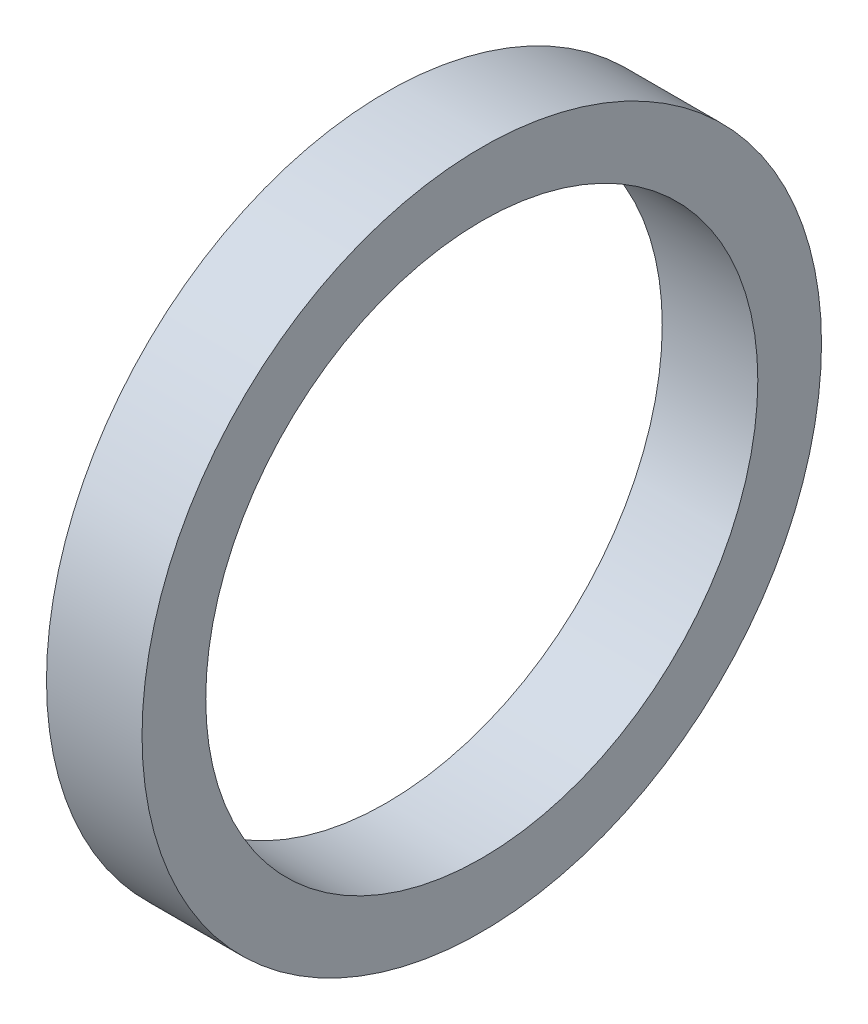
SolidWorks part; units mm, degrees
material "普通碳钢"
ref_plane "前视基准面" through (0, 0, 0) normal (0, 0, 1) x (1, 0, 0)
ref_plane "上视基准面" through (0, 0, 0) normal (0, 1, 0) x (1, 0, 0)
ref_plane "右视基准面" through (0, 0, 0) normal (1, 0, 0) x (0, 0, -1)
sketch "草图1" plane through (352.929, -174.9267, -1654.0002) normal (0, 0.6093, -0.7929) x (-1, 0, 0)
  line L0 (14.3824, -622.351) -> (7.3199, -622.351) construction
  line L2 (8.8199, -609.351) -> (13.3199, -609.351)
  line L3 (8.8199, -609.351) -> (8.8199, -606.351)
  line L4 (8.8199, -606.351) -> (13.3199, -606.351)
  line L5 (13.3199, -609.351) -> (13.3199, -606.351)
  dimension "D1" = 4.5
  dimension "D2" = 13
  dimension "D3" = 3
revolve "旋转1" add sketch "草图1" angle 360 about L0
